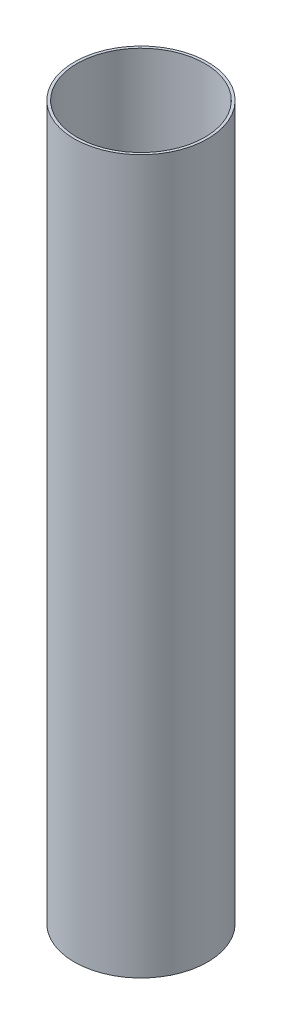
SolidWorks part; units mm, degrees
material "Wildman Fiberglass"
ref_plane "Front Plane" through (0, 0, 0) normal (0, 0, 1) x (1, 0, 0)
ref_plane "Top Plane" through (0, 0, 0) normal (0, 1, 0) x (1, 0, 0)
ref_plane "Right Plane" through (0, 0, 0) normal (1, 0, 0) x (0, 0, -1)
sketch "Sketch1" plane through (0, 0, 0) normal (0, 1, 0) x (1, 0, 0)
  circle A0 centre (0, 0) radius 27.3304
  circle A1 centre (0, 0) radius 28.4734
  dimension "D1" = 56.9468
  dimension "D2" = 54.6608
extrude "Boss-Extrude1" add sketch "Sketch1" along normal blind 304.8
equation "\"Length\"= 12"
equation "\"D1@Boss-Extrude1\"=\"Length\""
